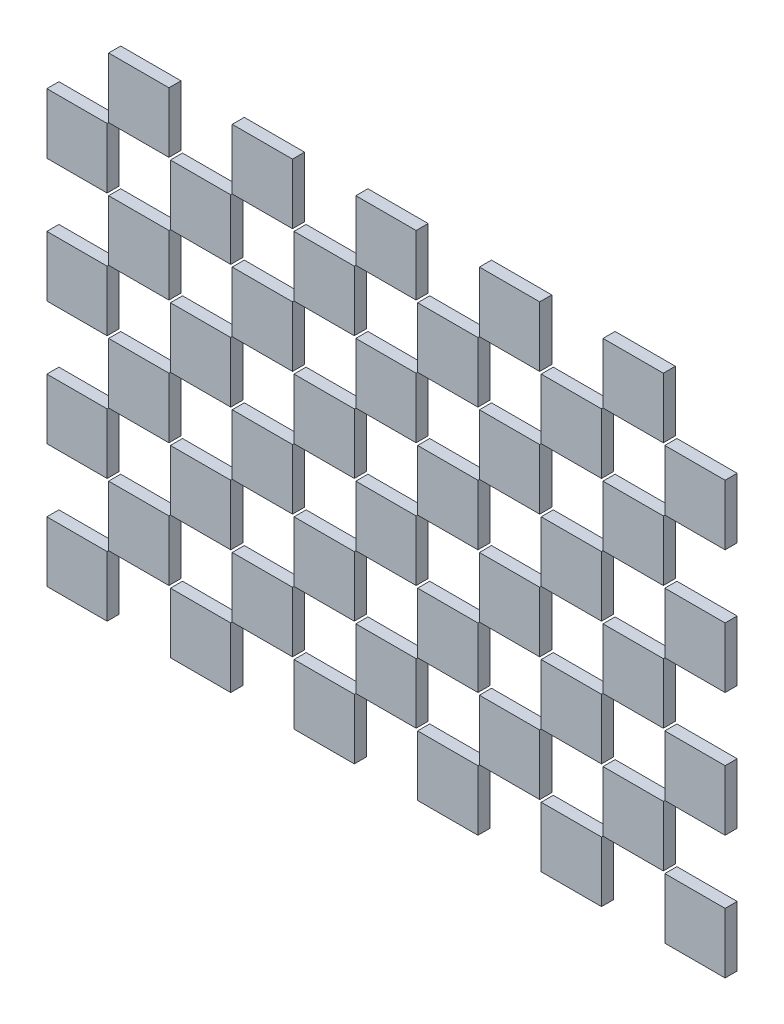
SolidWorks part; units mm, degrees
ref_plane "前视基准面" through (0, 0, 0) normal (0, 0, 1) x (1, 0, 0)
ref_plane "上视基准面" through (0, 0, 0) normal (0, 1, 0) x (1, 0, 0)
ref_plane "右视基准面" through (0, 0, 0) normal (1, 0, 0) x (0, 0, -1)
other "Configuration Table"
sketch "草图1" plane through (0, 0, 0) normal (0, 0, 1) x (1, 0, 0)
  line L1 (-6.7053, 8.1158) -> (-4.7053, 8.1158)
  line L2 (-6.7053, 8.1158) -> (-6.7053, 6.1158)
  line L3 (-6.7053, 6.1158) -> (-4.7053, 6.1158)
  line L4 (-4.7053, 8.1158) -> (-4.7053, 6.1158)
  dimension "D1" = 2
  dimension "D2" = 2
extrude "凸台-拉伸1" add sketch "草图1" along normal blind 0.4
pattern_linear "阵列(线性)1" count 4 spacing 4.1 along (0, 1, 0) count 6 spacing 4.1 along (1, 0, 0) of "凸台-拉伸1"
sketch "草图2" plane through (0, 0, 0) normal (0, 0, 1) x (1, 0, 0)
  line L5 (-4.7053, 10.2158) -> (-2.6053, 8.1158) construction
  line L6 (-2.6053, 10.2158) -> (-4.7053, 8.1158) construction
  line L7 (-4.6553, 8.1658) -> (-2.6553, 8.1658)
  line L8 (-4.6553, 8.1658) -> (-4.6553, 10.1658)
  line L9 (-4.6553, 10.1658) -> (-2.6553, 10.1658)
  line L10 (-2.6553, 8.1658) -> (-2.6553, 10.1658)
  line L11 (-4.6553, 8.1658) -> (-2.6553, 10.1658) construction
  line L12 (-4.6553, 10.1658) -> (-2.6553, 8.1658) construction
  point P0 (-3.6553, 9.1658)
  dimension "D1" = 2
extrude "凸台-拉伸2" add sketch "草图2" along normal blind 0.4 separate body
pattern_linear "阵列(线性)2" count 4 spacing 4.1 along (0, 1, 0) count 5 spacing 4.1 along (1, 0, 0) of "凸台-拉伸2"
